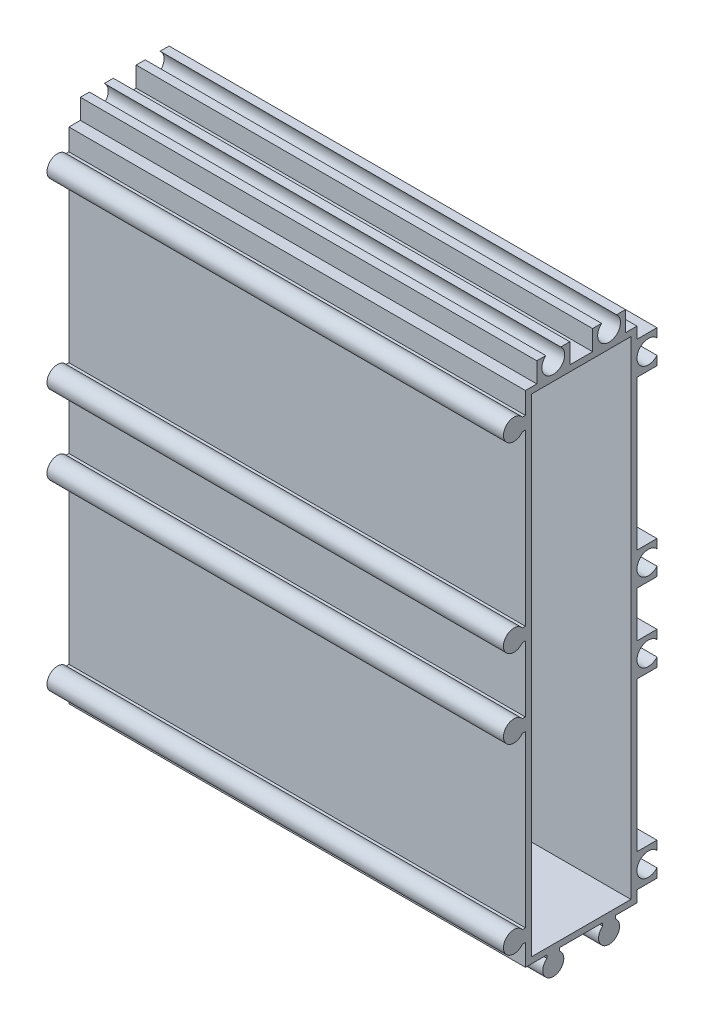
SolidWorks part; units mm, degrees
ref_plane "Спереди" through (0, 0, 0) normal (0, 0, 1) x (1, 0, 0)
ref_plane "Сверху" through (0, 0, 0) normal (0, 1, 0) x (1, 0, 0)
ref_plane "Справа" through (0, 0, 0) normal (1, 0, 0) x (0, 0, -1)
ref_plane "Плоскость4" through (90, 0, 0) normal (1, 0, 0) x (0, 0, -1)
sketch "Эскиз1" plane through (90, 0, 0) normal (1, 0, 0) x (0, 0, -1)
  line L0 (6.75, 40.9062) -> (6.75, 135.75)
  line L1 (6.75, 135.75) -> (-11.5938, 135.75)
  line L2 (-11.5938, 133.25) -> (-11, 133.25)
  line L3 (-11, 133.25) -> (-11, 99.75)
  line L4 (-11, 99.75) -> (-11.5938, 99.75)
  line L5 (-11.5938, 97.25) -> (-11, 97.25)
  line L6 (-11, 97.25) -> (-11, 84.25)
  line L7 (-11, 84.25) -> (-11.5938, 84.25)
  line L8 (-11.5938, 81.75) -> (-11, 81.75)
  line L9 (-11, 81.75) -> (-11, 48.25)
  line L10 (-11, 48.25) -> (-11.5938, 48.25)
  line L11 (-11.5938, 45.75) -> (-11, 45.75)
  line L12 (-11, 45.75) -> (-11, 41.5)
  line L13 (-11, 41.5) -> (-6.75, 41.5)
  line L14 (-6.75, 41.5) -> (-6.75, 40.9062)
  line L15 (-4.25, 40.9062) -> (-4.25, 41.5)
  line L16 (-4.25, 41.5) -> (4.25, 41.5)
  line L17 (4.25, 41.5) -> (4.25, 40.9062)
  arc A0 (-11.5938, 135.75) -> (-11.5938, 133.25) centre (-13.25, 134.5) ccw
  arc A1 (-11.5938, 99.75) -> (-11.5938, 97.25) centre (-13.25, 98.5) ccw
  arc A2 (-11.5938, 84.25) -> (-11.5938, 81.75) centre (-13.25, 83) ccw
  arc A3 (-11.5938, 48.25) -> (-11.5938, 45.75) centre (-13.25, 47) ccw
  arc A4 (-6.75, 40.9062) -> (-4.25, 40.9062) centre (-5.5, 39.25) ccw
  arc A5 (4.25, 40.9062) -> (6.75, 40.9062) centre (5.5, 39.25) ccw
extrude "Бобышка-Вытянуть1" add sketch "Эскиз1" against normal blind 90
sketch "Эскиз2" plane through (0, 135.75, 0) normal (0, 1, 0) x (-1, 0, 0)
  line L0 (-90, -6.75) -> (-90, 11)
  line L1 (-90, 11) -> (0, 11)
  line L2 (0, 11) -> (0, -6.75)
  line L3 (0, -6.75) -> (-90, -6.75)
extrude "Бобышка-Вытянуть2" add sketch "Эскиз2" along normal blind 8.2
sketch "Эскиз3" plane through (0, 0, -6.75) normal (0, 0, -1) x (-1, 0, 0)
  line L0 (-90, 41.5) -> (-90, 143.95)
  line L1 (-90, 143.95) -> (0, 143.95)
  line L2 (0, 143.95) -> (0, 41.5)
  line L3 (0, 41.5) -> (-90, 41.5)
extrude "Бобышка-Вытянуть3" add sketch "Эскиз3" along normal blind 8.2
sketch "Эскиз4" plane through (0, 0, 0) normal (-1, 0, 0) x (0, 0, 1)
  line L0 (-14.95, 41.5) -> (-11, 41.5)
  line L1 (-11, 41.5) -> (-11, 43.75)
  line L2 (-11, 43.75) -> (-14.95, 43.75)
  line L3 (-14.95, 43.75) -> (-14.95, 41.5)
extrude "Вырез-Вытянуть1" cut sketch "Эскиз4" against normal through all
sketch "Эскиз5" plane through (0, 0, 0) normal (-1, 0, 0) x (0, 0, 1)
  line L0 (-14.95, 50.25) -> (-11, 50.25)
  line L1 (-11, 50.25) -> (-11, 79.75)
  line L2 (-11, 79.75) -> (-14.95, 79.75)
  line L3 (-14.95, 79.75) -> (-14.95, 50.25)
extrude "Вырез-Вытянуть2" cut sketch "Эскиз5" against normal through all
sketch "Эскиз6" plane through (0, 0, 0) normal (-1, 0, 0) x (0, 0, 1)
  line L0 (-14.95, 86.25) -> (-11, 86.25)
  line L1 (-11, 86.25) -> (-11, 95.25)
  line L2 (-11, 95.25) -> (-14.95, 95.25)
  line L3 (-14.95, 95.25) -> (-14.95, 86.25)
extrude "Вырез-Вытянуть3" cut sketch "Эскиз6" against normal through all
sketch "Эскиз7" plane through (0, 0, 0) normal (-1, 0, 0) x (0, 0, 1)
  line L0 (-14.95, 101.75) -> (-11, 101.75)
  line L1 (-11, 101.75) -> (-11, 131.25)
  line L2 (-11, 131.25) -> (-14.95, 131.25)
  line L3 (-14.95, 131.25) -> (-14.95, 101.75)
extrude "Вырез-Вытянуть4" cut sketch "Эскиз7" against normal through all
sketch "Эскиз8" plane through (0, 0, 0) normal (-1, 0, 0) x (0, 0, 1)
  line L0 (-14.95, 143.95) -> (-14.95, 137.75)
  line L1 (-14.95, 137.75) -> (-11, 137.75)
  line L2 (-11, 137.75) -> (-11, 143.95)
  line L3 (-11, 143.95) -> (-14.95, 143.95)
extrude "Вырез-Вытянуть5" cut sketch "Эскиз8" against normal through all
sketch "Эскиз9" plane through (0, 0, 0) normal (-1, 0, 0) x (0, 0, 1)
  line L0 (-11, 143.95) -> (-11, 140)
  line L1 (-11, 140) -> (-8.75, 140)
  line L2 (-8.75, 140) -> (-8.75, 143.95)
  line L3 (-8.75, 143.95) -> (-11, 143.95)
extrude "Вырез-Вытянуть6" cut sketch "Эскиз9" against normal through all
sketch "Эскиз10" plane through (0, 0, 0) normal (-1, 0, 0) x (0, 0, 1)
  line L0 (-2.25, 143.95) -> (-2.25, 140)
  line L1 (-2.25, 140) -> (2.25, 140)
  line L2 (2.25, 140) -> (2.25, 143.95)
  line L3 (2.25, 143.95) -> (-2.25, 143.95)
extrude "Вырез-Вытянуть7" cut sketch "Эскиз10" against normal through all
sketch "Эскиз11" plane through (0, 0, 0) normal (-1, 0, 0) x (0, 0, 1)
  line L0 (11, 143.95) -> (8.75, 143.95)
  line L1 (8.75, 143.95) -> (8.75, 140)
  line L2 (8.75, 140) -> (11, 140)
  line L3 (11, 140) -> (11, 143.95)
extrude "Вырез-Вытянуть8" cut sketch "Эскиз11" against normal through all
sketch "Эскиз12" plane through (90, 0, 0) normal (1, 0, 0) x (0, 0, -1)
  line L0 (9.8, 138.8) -> (-9.8, 138.8)
  line L1 (-9.8, 138.8) -> (-9.8, 42.7)
  line L2 (-9.8, 42.7) -> (9.8, 42.7)
  line L3 (9.8, 42.7) -> (9.8, 138.8)
  line L4 (-11, 133.25) -> (-11, 99.75) construction
  line L5 (2.25, 140) -> (-2.25, 140) construction
  line L6 (11, 101.75) -> (11, 131.25) construction
  line L7 (-4.25, 41.5) -> (4.25, 41.5) construction
  point P10 (0, 42.7)
  dimension "D1" = 1.2
  dimension "D2" = 1.2
  dimension "D3" = 1.2
  dimension "D4" = 1.2
extrude "Вырез-Вытянуть9" cut sketch "Эскиз12" against normal blind 86.2
hole_wizard "Диаметр отверстия Ø8.3 (8.3)1" [suppressed] positions "Эскиз14" profile "Эскиз13" hole size "Ø8.3" standard "Ansi Metric"
sketch "Эскиз14" plane through (0, 0, 0) normal (-1, 0, 0) x (0, 0, 1)
  point P0 (0, 90)
sketch "Эскиз13" plane through (0, 90, 0) normal (0, 1, 0) x (0, 0, 1)
  line L0 (0, 0) -> (0, 3.2)
  line L1 (0, 3.2) -> (4.15, 3.2)
  line L2 (4.15, 3.2) -> (4.15, 0)
  line L5 (4.15, 0) -> (0, 0)
  line L10 (0, 3.2) -> (-4.15, 3.2) construction
  line L11 (0, -6.35) -> (0, 107.95) construction
  dimension "Диаметр отверстия" = 8.3
  dimension "Глубина отверстия" = 3.2
  dimension "Угол заточки сверла" = 180
hole_wizard "Диаметр отверстия Ø4.5 (4.5)1" positions "Эскиз16" profile "Эскиз15" hole size "Ø4.5" standard "Ansi Metric"
sketch "Эскиз16" plane through (0, 0, 0) normal (-1, 0, 0) x (0, 0, 1)
  point P0 (-13.25, 47)
  point P1 (-13.25, 83)
  point P2 (-13.25, 98.5)
  point P3 (-13.25, 134.5)
  point P4 (-5.5, 142.25)
  point P5 (5.5, 142.25)
sketch "Эскиз15" plane through (0, 47, -13.25) normal (0, 1, 0) x (0, 0, 1)
  line L0 (0, 0) -> (0, 90)
  line L1 (0, 90) -> (2.25, 90)
  line L2 (2.25, 90) -> (2.25, 0)
  line L5 (2.25, 0) -> (0, 0)
  line L11 (0, -6.35) -> (0, 107.95) construction
  dimension "Диаметр сквозного отверстия" = 4.5
  dimension "Глубина сквозного отверстия" = 90
hole_wizard "Диаметр отверстия Ø2.5 (2.5)1" positions "Эскиз18" profile "Эскиз17" hole size "Ø2.5" standard "Ansi Metric"
sketch "Эскиз18" plane through (90, 0, 0) normal (1, 0, 0) x (0, 0, -1)
  point P0 (-13.25, 98.5)
  point P1 (-13.25, 134.5)
  point P2 (-13.25, 47)
  point P3 (-13.25, 83)
  point P4 (5.5, 39.25)
  point P5 (-5.5, 39.25)
sketch "Эскиз17" plane through (90, 98.5, 13.25) normal (0, 1, 0) x (0, 0, -1)
  line L0 (0, 0) -> (0, 90)
  line L1 (0, 90) -> (1.25, 90)
  line L2 (1.25, 90) -> (1.25, 0)
  line L5 (1.25, 0) -> (0, 0)
  line L11 (0, -6.35) -> (0, 107.95) construction
  dimension "Диаметр сквозного отверстия" = 2.5
  dimension "Глубина сквозного отверстия" = 90
sketch "Эскиз19" [suppressed] plane through (0, 0, 0) normal (-1, 0, 0) x (0, 0, 1)
  circle A0 centre (0, 90) radius 4.5031
extrude "Бобышка-Вытянуть4" [suppressed] add sketch "Эскиз19" against normal blind 3
sketch "Эскиз20" plane through (90, 0, 0) normal (1, 0, 0) x (0, 0, -1)
  circle A0 centre (-13.25, 134.5) radius 1.6499
  circle A1 centre (-13.25, 98.5) radius 1.6606
  circle A2 centre (-13.25, 83) radius 1.4307
  circle A3 centre (-13.25, 47) radius 1.5733
  circle A4 centre (-5.5, 39.25) radius 1.502
  circle A5 centre (5.5, 39.25) radius 1.538
extrude "Бобышка-Вытянуть5" add sketch "Эскиз20" against normal blind 90
equation "\"D2@Эскиз12\"=\"D1@Эскиз12\""
equation "\"D3@Эскиз12\"=\"D1@Эскиз12\""
equation "\"D4@Эскиз12\"=\"D1@Эскиз12\""
